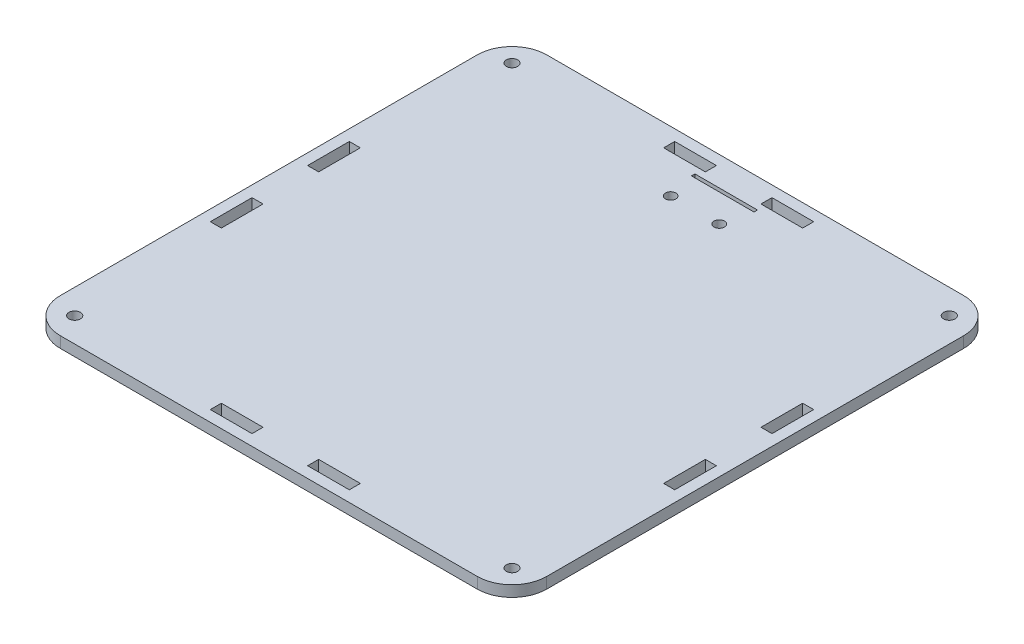
SolidWorks part; units mm, degrees
ref_plane "Front Plane" through (0, 0, 0) normal (0, 0, 1) x (1, 0, 0)
ref_plane "Top Plane" through (0, 0, 0) normal (0, 1, 0) x (1, 0, 0)
ref_plane "Right Plane" through (0, 0, 0) normal (1, 0, 0) x (0, 0, -1)
sketch "Sketch1" plane through (0, 0, 0) normal (0, 1, 0) x (1, 0, 0)
  line L0 (-70, 0) -> (70, 0) construction
  line L1 (-70, 70) -> (70, 70)
  line L2 (-70, 70) -> (-70, -70)
  line L3 (-70, -70) -> (70, -70)
  line L4 (70, 70) -> (70, -70)
  line L11 (0, 70) -> (0, -70) construction
  line L22 (-66.825, -8) -> (-66.825, -20)
  line L23 (63.65, -8) -> (66.825, -8)
  line L24 (63.65, -8) -> (63.65, -20)
  line L25 (63.65, -20) -> (66.825, -20)
  line L26 (66.825, -8) -> (66.825, -20)
  line L27 (8, -66.825) -> (20, -66.825)
  line L28 (8, -66.825) -> (8, -63.65)
  line L29 (8, -63.65) -> (20, -63.65)
  line L30 (20, -66.825) -> (20, -63.65)
  line L31 (-63.65, -20) -> (-66.825, -20)
  line L32 (-63.65, -8) -> (-63.65, -20)
  line L33 (-63.65, -8) -> (-66.825, -8)
  line L34 (-20, -66.825) -> (-20, -63.65)
  line L35 (-8, -63.65) -> (-20, -63.65)
  line L36 (-8, -66.825) -> (-8, -63.65)
  line L37 (-8, -66.825) -> (-20, -66.825)
  line L38 (66.825, 8) -> (66.825, 20)
  line L39 (63.65, 20) -> (66.825, 20)
  line L40 (63.65, 8) -> (63.65, 20)
  line L41 (63.65, 8) -> (66.825, 8)
  line L42 (20, 66.825) -> (20, 63.65)
  line L43 (8, 63.65) -> (20, 63.65)
  line L44 (8, 66.825) -> (8, 63.65)
  line L45 (8, 66.825) -> (20, 66.825)
  line L46 (-8, 66.825) -> (-20, 66.825)
  line L47 (-8, 66.825) -> (-8, 63.65)
  line L48 (-8, 63.65) -> (-20, 63.65)
  line L49 (-20, 66.825) -> (-20, 63.65)
  line L50 (-63.65, 8) -> (-66.825, 8)
  line L51 (-63.65, 8) -> (-63.65, 20)
  line L52 (-63.65, 20) -> (-66.825, 20)
  line L53 (-66.825, 8) -> (-66.825, 20)
  line L54 (-70, -70) -> (70, 70) construction
  line L55 (-70, 70) -> (70, -70) construction
  line L57 (-9, 60.65) -> (9, 60.65)
  line L58 (-9, 60.65) -> (-9, 61.65)
  line L59 (-9, 61.65) -> (9, 61.65)
  line L60 (9, 60.65) -> (9, 61.65)
  line L61 (-9, 60.65) -> (9, 61.65) construction
  line L62 (-9, 61.65) -> (9, 60.65) construction
  circle A10 centre (62.9289, -62.9289) radius 1.65
  circle A11 centre (62.9289, 62.9289) radius 1.65
  circle A12 centre (-62.9289, -62.9289) radius 1.65
  circle A13 centre (-62.9289, 62.9289) radius 1.65
  circle A14 centre (7, 52.65) radius 1.5
  circle A15 centre (-7, 52.65) radius 1.5
  point P0 (0, 0)
  point P8 (0, 61.15)
  point P11 (0, 0)
  dimension "D5" = 3.175
  dimension "D6" = 3
  dimension "D27" = 3.3
  dimension "D3" = 3.175
  dimension "D4" = 3.175
  dimension "D7" = 7
  dimension "D8" = 18
  dimension "D9" = 1
  dimension "D10" = 2
  dimension "D11" = 8
  dimension "D13" = 140
  dimension "D14" = 140
  dimension "D21" = 3.175
  dimension "D22" = 12
  dimension "D23" = 12
  dimension "D24" = 8
  dimension "D25" = 8
  dimension "D26" = 10
extrude "Boss-Extrude1" add sketch "Sketch1" along normal blind 3.175
fillet "Fillet1" radius 10 4 edges at (70, 1.5875, -70) (70, 1.5875, 70) (-70, 1.5875, 70) (-70, 1.5875, -70)
